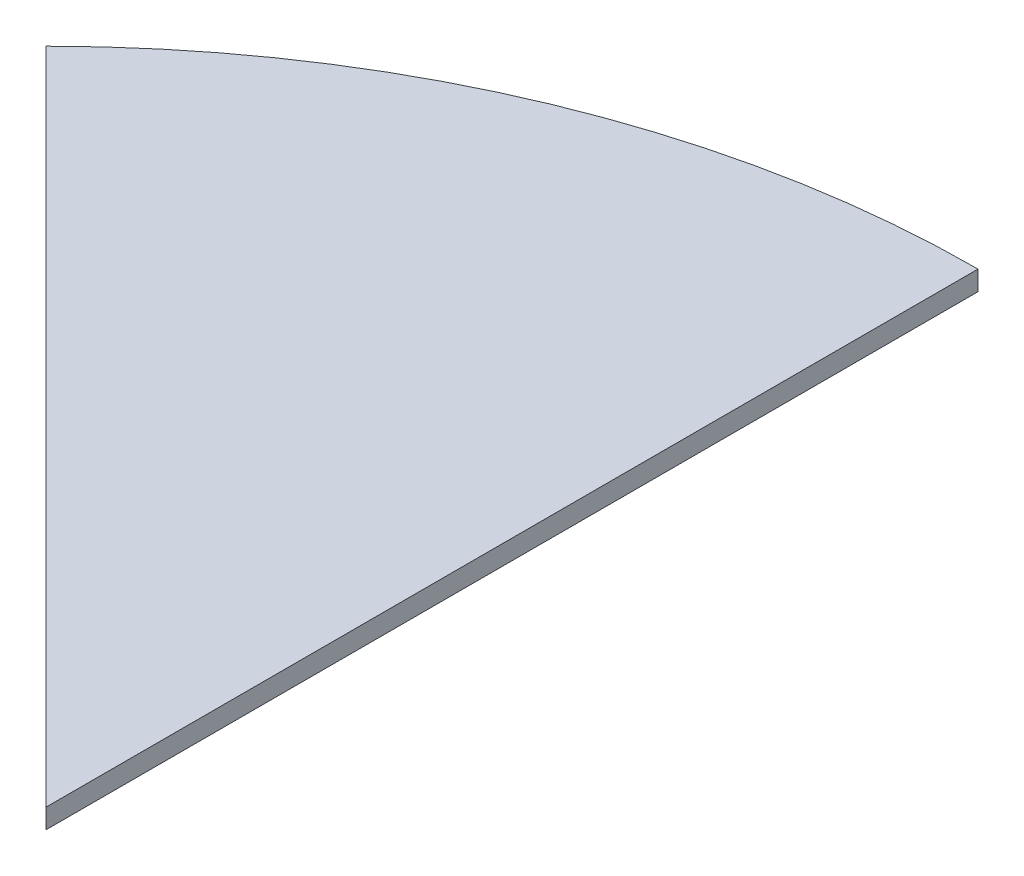
SolidWorks part; units mm, degrees
ref_plane "Front Plane" through (0, 0, 0) normal (0, 0, 1) x (1, 0, 0)
ref_plane "Top Plane" through (0, 0, 0) normal (0, 1, 0) x (1, 0, 0)
ref_plane "Right Plane" through (0, 0, 0) normal (1, 0, 0) x (0, 0, -1)
sketch "Sketch1" plane through (0, 0, 0) normal (0, 1, 0) x (1, 0, 0)
  line L0 (0, 950) -> (0, 0)
  line L1 (0, 0) -> (-671.7514, 671.7514)
  arc A0 (0, 950) -> (-671.7514, 671.7514) centre (0, 0) ccw
  dimension "D1" = 1900
extrude "Extrude1" add sketch "Sketch1" along normal blind 20
